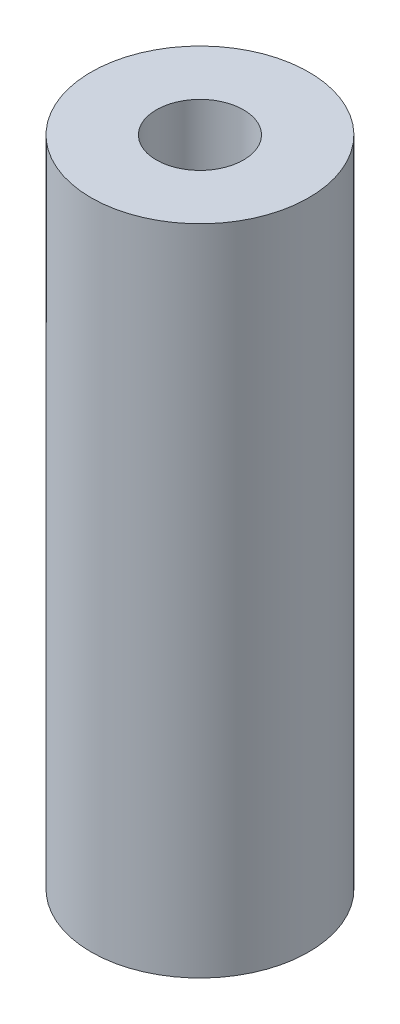
SolidWorks part; units mm, degrees
material "Melamine resin"
ref_plane "Front Plane" through (0, 0, 0) normal (0, 0, 1) x (1, 0, 0)
ref_plane "Top Plane" through (0, 0, 0) normal (0, 1, 0) x (1, 0, 0)
ref_plane "Right Plane" through (0, 0, 0) normal (1, 0, 0) x (0, 0, -1)
sketch "Sketch1" plane through (0, 0, 0) normal (0, 1, 0) x (1, 0, 0)
  circle A0 centre (0, 0) radius 3.175
  circle A1 centre (0, 0) radius 1.27
  dimension "D1" = 6.35
  dimension "D2" = 2.54
extrude "Boss-Extrude1" add sketch "Sketch1" along normal blind 19.05
